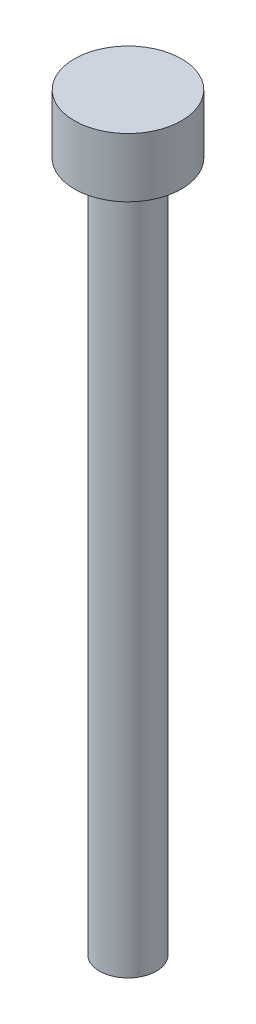
SolidWorks part; units mm, degrees
ref_plane "Front Plane" through (0, 0, 0) normal (0, 0, 1) x (1, 0, 0)
ref_plane "Top Plane" through (0, 0, 0) normal (0, 1, 0) x (1, 0, 0)
ref_plane "Right Plane" through (0, 0, 0) normal (1, 0, 0) x (0, 0, -1)
sketch "Sketch1" plane through (0, 0, 0) normal (0, 1, 0) x (1, 0, 0)
  circle A0 centre (0, 0) radius 2.72
  dimension "D1" = 5.44
extrude "Boss-Extrude1" add sketch "Sketch1" along normal blind 3
sketch "Sketch2" plane through (0, 0, 0) normal (0, -1, 0) x (1, 0, 0)
  circle A0 centre (0, 0) radius 1.44
  dimension "D1" = 2.88
extrude "Boss-Extrude2" add sketch "Sketch2" along normal blind 35
